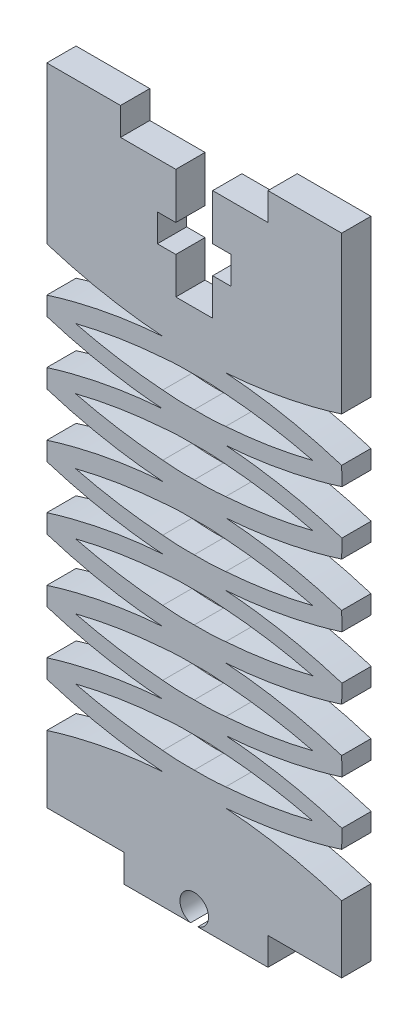
SolidWorks part; units mm, degrees
ref_plane "Front Plane" through (0, 0, 0) normal (0, 0, 1) x (1, 0, 0)
ref_plane "Top Plane" through (0, 0, 0) normal (0, 1, 0) x (1, 0, 0)
ref_plane "Right Plane" through (0, 0, 0) normal (1, 0, 0) x (0, 0, -1)
sketch "Sketch1" plane through (0, 0, 0) normal (0, 0, 1) x (1, 0, 0)
  line L0 (16, 85.8057) -> (16, -11.2855) construction
  line L1 (0, 0) -> (8.3703, 0)
  line L2 (0, 0) -> (0, 7.2655)
  line L3 (0, 70) -> (8, 70)
  line L4 (24, 70) -> (32, 70)
  line L5 (24, 70) -> (24, 67)
  line L6 (24, 67) -> (18, 67)
  line L7 (8, 67) -> (8, 70)
  line L8 (14, 67) -> (14, 62)
  line L9 (14, 55) -> (18, 55)
  line L10 (18, 55) -> (18, 59)
  line L11 (32, 70) -> (32, 53)
  line L12 (12, 62) -> (14, 62)
  line L13 (12, 62) -> (12, 59)
  line L14 (12, 59) -> (14, 59)
  line L15 (20, 62) -> (20, 59)
  line L16 (14, 67) -> (8, 67)
  line L17 (18, 62) -> (20, 62)
  line L18 (14, 59) -> (14, 55)
  line L19 (18, 62) -> (18, 67)
  line L20 (18, 59) -> (20, 59)
  line L21 (40.1078, 53) -> (-4.0863, 53) construction
  line L22 (24, 0) -> (24, -3)
  line L23 (24, -3) -> (16.3905, -3)
  line L24 (8.3703, -3) -> (8.3703, 0)
  line L25 (24, 0) -> (32, 0)
  line L26 (15.6095, -3) -> (8.3703, -3)
  line L27 (26, 0) -> (26, -11.2855) construction
  line L28 (26, 85.8057) -> (26, 8.7935) construction
  line L29 (32, 12.0848) -> (32.0289, 14.0848)
  line L30 (6, 85.8057) -> (6, 8.7935) construction
  line L31 (0, 53) -> (0, 70)
  line L32 (32.0289, 18.904) -> (32, 20.904)
  line L33 (32.0289, 46.1808) -> (32, 48.1808)
  line L34 (32, 5.3702) -> (32, 7.2655)
  line L35 (0, 48.1808) -> (0, 46.1718)
  line L36 (32, 34.5424) -> (32.0289, 32.5424)
  line L37 (32.0289, 27.7232) -> (32, 25.7232)
  line L38 (0, 41.3706) -> (0, 39.3616)
  line L39 (32, 5.3702) -> (32, 0)
  line L40 (0, 34.5424) -> (0, 32.5333)
  line L41 (0, 27.7322) -> (0, 25.7232)
  line L43 (0, 20.904) -> (0, 18.8949)
  line L44 (0, 14.0938) -> (0, 12.0848)
  line L46 (32.0289, 41.3616) -> (32, 39.3616)
  arc A0 (16.3905, -3) -> (15.6095, -3) centre (16, -1.5) ccw
  spline S0 degree 3 poles (32, 53) (27.8985, 51.7075) (23.6915, 50.9043) (19.4175, 50.5904) knots 0 0 0 0 0.790279 0.790279 0.790279 0.790279
  spline S1 degree 3 poles (32, 48.1808) (27.8985, 49.4733) (23.6915, 50.2765) (19.4175, 50.5904) knots 0 0 0 0 0.790279 0.790279 0.790279 0.790279
  spline S2 degree 3 poles (28.8769, 47.068) (26.7129, 47.6104) (23.5714, 48.2011) (20.3909, 48.5189) (19.4167, 48.5904) knots 0.199989 0.199989 0.199989 0.199989 0.610157 0.790279 0.790279 0.790279 0.790279
  spline S3 degree 2 poles (19.4167, 48.5904) (17.7133, 48.7693) (16, 48.7209) knots 0 0 0 1 1 1
  spline S4 degree 2 poles (19.4167, 45.5457) (17.7133, 45.3668) (16, 45.4152) knots 0 0 0 1 1 1
  spline S5 degree 3 poles (28.8769, 47.068) (26.7129, 46.5257) (23.5714, 45.935) (20.3909, 45.6172) (19.4167, 45.5457) knots 0.199989 0.199989 0.199989 0.199989 0.610157 0.790279 0.790279 0.790279 0.790279
  spline S6 degree 3 poles (32.0289, 41.3616) (27.8948, 42.6541) (23.6907, 43.4573) (19.4167, 43.7712) knots 0 0 0 0 0.790279 0.790279 0.790279 0.790279
  spline S7 degree 3 poles (32.0289, 46.1808) (27.8948, 44.8883) (23.6907, 44.0851) (19.4167, 43.7712) knots 0 0 0 0 0.790279 0.790279 0.790279 0.790279
  spline S8 degree 2 poles (19.4167, 41.9967) (17.7133, 42.1756) (16, 42.1272) knots 0 0 0 1 1 1
  spline S9 degree 3 poles (28.8769, 40.4743) (26.7129, 41.0166) (23.5714, 41.6074) (20.3909, 41.9251) (19.4167, 41.9967) knots 0.199989 0.199989 0.199989 0.199989 0.610157 0.790279 0.790279 0.790279 0.790279
  spline S10 degree 2 poles (19.4167, 38.952) (17.7133, 38.7731) (16, 38.8214) knots 0 0 0 1 1 1
  spline S11 degree 3 poles (28.8769, 40.4743) (26.7129, 39.932) (23.5714, 39.3413) (20.3909, 39.0235) (19.4167, 38.952) knots 0.199989 0.199989 0.199989 0.199989 0.610157 0.790279 0.790279 0.790279 0.790279
  spline S12 degree 3 poles (32, 39.3616) (27.8985, 38.0691) (23.6915, 37.2659) (19.4175, 36.952) knots 0 0 0 0 0.790279 0.790279 0.790279 0.790279
  spline S13 degree 3 poles (32.0289, 32.5424) (27.8948, 31.2499) (23.6907, 30.4467) (19.4167, 30.1328) knots 0 0 0 0 0.790279 0.790279 0.790279 0.790279
  spline S14 degree 2 poles (19.4167, 31.9073) (17.7133, 31.7284) (16, 31.7767) knots 0 0 0 1 1 1
  spline S15 degree 3 poles (28.8769, 33.4296) (26.7129, 32.8873) (23.5714, 32.2966) (20.3909, 31.9788) (19.4167, 31.9073) knots 0.199989 0.199989 0.199989 0.199989 0.610157 0.790279 0.790279 0.790279 0.790279
  spline S16 degree 2 poles (19.4167, 34.952) (17.7133, 35.1309) (16, 35.0825) knots 0 0 0 1 1 1
  spline S17 degree 3 poles (28.8769, 33.4296) (26.7129, 33.9719) (23.5714, 34.5627) (20.3909, 34.8804) (19.4167, 34.952) knots 0.199989 0.199989 0.199989 0.199989 0.610157 0.790279 0.790279 0.790279 0.790279
  spline S18 degree 3 poles (32, 34.5424) (27.8985, 35.8349) (23.6915, 36.6381) (19.4175, 36.952) knots 0 0 0 0 0.790279 0.790279 0.790279 0.790279
  spline S19 degree 3 poles (32.0289, 18.904) (27.8948, 17.6114) (23.6907, 16.8082) (19.4167, 16.4944) knots 0 0 0 0 0.790279 0.790279 0.790279 0.790279
  spline S20 degree 2 poles (19.4167, 28.3583) (17.7133, 28.5371) (16, 28.4888) knots 0 0 0 1 1 1
  spline S21 degree 2 poles (19.4167, 25.3136) (17.7133, 25.1347) (16, 25.183) knots 0 0 0 1 1 1
  spline S22 degree 2 poles (19.4167, 21.3136) (17.7133, 21.4924) (16, 21.4441) knots 0 0 0 1 1 1
  spline S23 degree 2 poles (19.4167, 18.2689) (17.7133, 18.09) (16, 18.1383) knots 0 0 0 1 1 1
  spline S24 degree 3 poles (28.8769, 19.7912) (26.7129, 19.2489) (23.5714, 18.6582) (20.3909, 18.3404) (19.4167, 18.2689) knots 0.199989 0.199989 0.199989 0.199989 0.610157 0.790279 0.790279 0.790279 0.790279
  spline S25 degree 3 poles (28.8769, 19.7912) (26.7129, 20.3335) (23.5714, 20.9243) (20.3909, 21.242) (19.4167, 21.3136) knots 0.199989 0.199989 0.199989 0.199989 0.610157 0.790279 0.790279 0.790279 0.790279
  spline S26 degree 3 poles (32, 20.904) (27.8985, 22.1965) (23.6915, 22.9997) (19.4175, 23.3136) knots 0 0 0 0 0.790279 0.790279 0.790279 0.790279
  spline S27 degree 3 poles (32.0289, 27.7232) (27.8948, 29.0157) (23.6907, 29.8189) (19.4167, 30.1328) knots 0 0 0 0 0.790279 0.790279 0.790279 0.790279
  spline S28 degree 3 poles (28.8769, 26.8359) (26.7129, 27.3782) (23.5714, 27.969) (20.3909, 28.2867) (19.4167, 28.3583) knots 0.199989 0.199989 0.199989 0.199989 0.610157 0.790279 0.790279 0.790279 0.790279
  spline S29 degree 3 poles (28.8769, 26.8359) (26.7129, 26.2936) (23.5714, 25.7029) (20.3909, 25.3851) (19.4167, 25.3136) knots 0.199989 0.199989 0.199989 0.199989 0.610157 0.790279 0.790279 0.790279 0.790279
  spline S30 degree 3 poles (32, 25.7232) (27.8985, 24.4306) (23.6915, 23.6274) (19.4175, 23.3136) knots 0 0 0 0 0.790279 0.790279 0.790279 0.790279
  spline S31 degree 3 poles (0, 14.0938) (3.1825, 15.087) (7.361, 15.9984) (11.6091, 16.4228) (12.5833, 16.4944) knots 0.001844 0.001844 0.001844 0.001844 0.610157 0.790279 0.790279 0.790279 0.790279
  spline S32 degree 3 poles (3.1231, 13.1975) (5.2871, 13.7398) (8.4286, 14.3306) (11.6091, 14.6483) (12.5833, 14.7198) knots 0.199989 0.199989 0.199989 0.199989 0.610157 0.790279 0.790279 0.790279 0.790279
  spline S33 degree 2 poles (12.5833, 14.7198) (14.2867, 14.8987) (16, 14.8504) knots 0 0 0 1 1 1
  spline S34 degree 3 poles (3.1231, 13.1975) (5.2871, 12.6552) (8.4286, 12.0644) (11.6091, 11.7467) (12.5833, 11.6752) knots 0.199989 0.199989 0.199989 0.199989 0.610157 0.790279 0.790279 0.790279 0.790279
  spline S35 degree 2 poles (12.5833, 11.6752) (14.2867, 11.4963) (16, 11.5446) knots 0 0 0 1 1 1
  spline S36 degree 3 poles (32, 7.2655) (27.8985, 8.5581) (23.6915, 9.3613) (19.4175, 9.6752) knots 0 0 0 0 0.790279 0.790279 0.790279 0.790279
  spline S37 degree 3 poles (32, 12.0848) (27.8985, 10.7922) (23.6915, 9.989) (19.4175, 9.6752) knots 0 0 0 0 0.790279 0.790279 0.790279 0.790279
  spline S38 degree 2 poles (19.4167, 11.6752) (17.7133, 11.4963) (16, 11.5446) knots 0 0 0 1 1 1
  spline S39 degree 3 poles (28.8769, 13.1975) (26.7129, 12.6552) (23.5714, 12.0644) (20.3909, 11.7467) (19.4167, 11.6752) knots 0.199989 0.199989 0.199989 0.199989 0.610157 0.790279 0.790279 0.790279 0.790279
  spline S40 degree 2 poles (19.4167, 14.7198) (17.7133, 14.8987) (16, 14.8504) knots 0 0 0 1 1 1
  spline S41 degree 3 poles (28.8769, 13.1975) (26.7129, 13.7398) (23.5714, 14.3306) (20.3909, 14.6483) (19.4167, 14.7198) knots 0.199989 0.199989 0.199989 0.199989 0.610157 0.790279 0.790279 0.790279 0.790279
  spline S42 degree 3 poles (32.0289, 14.0848) (27.8948, 15.3773) (23.6907, 16.1805) (19.4167, 16.4944) knots 0 0 0 0 0.790279 0.790279 0.790279 0.790279
  spline S43 degree 3 poles (0, 12.0848) (4.1015, 10.7922) (8.3085, 9.989) (12.5825, 9.6752) knots 0 0 0 0 0.790279 0.790279 0.790279 0.790279
  spline S44 degree 3 poles (0, 7.2655) (4.1015, 8.5581) (8.3085, 9.3613) (12.5825, 9.6752) knots 0 0 0 0 0.790279 0.790279 0.790279 0.790279
  spline S45 degree 3 poles (0, 25.7232) (4.1015, 24.4306) (8.3085, 23.6274) (12.5825, 23.3136) knots 0 0 0 0 0.790279 0.790279 0.790279 0.790279
  spline S46 degree 3 poles (3.1231, 26.8359) (5.2871, 26.2936) (8.4286, 25.7029) (11.6091, 25.3851) (12.5833, 25.3136) knots 0.199989 0.199989 0.199989 0.199989 0.610157 0.790279 0.790279 0.790279 0.790279
  spline S47 degree 3 poles (3.1231, 26.8359) (5.2871, 27.3782) (8.4286, 27.969) (11.6091, 28.2867) (12.5833, 28.3583) knots 0.199989 0.199989 0.199989 0.199989 0.610157 0.790279 0.790279 0.790279 0.790279
  spline S48 degree 3 poles (0, 27.7322) (3.1825, 28.7254) (7.361, 29.6368) (11.6091, 30.0612) (12.5833, 30.1328) knots 0.001844 0.001844 0.001844 0.001844 0.610157 0.790279 0.790279 0.790279 0.790279
  spline S49 degree 3 poles (0, 20.904) (4.1015, 22.1965) (8.3085, 22.9997) (12.5825, 23.3136) knots 0 0 0 0 0.790279 0.790279 0.790279 0.790279
  spline S50 degree 3 poles (3.1231, 19.7912) (5.2871, 20.3335) (8.4286, 20.9243) (11.6091, 21.242) (12.5833, 21.3136) knots 0.199989 0.199989 0.199989 0.199989 0.610157 0.790279 0.790279 0.790279 0.790279
  spline S51 degree 3 poles (3.1231, 19.7912) (5.2871, 19.2489) (8.4286, 18.6582) (11.6091, 18.3404) (12.5833, 18.2689) knots 0.199989 0.199989 0.199989 0.199989 0.610157 0.790279 0.790279 0.790279 0.790279
  spline S52 degree 2 poles (12.5833, 18.2689) (14.2867, 18.09) (16, 18.1383) knots 0 0 0 1 1 1
  spline S53 degree 2 poles (12.5833, 21.3136) (14.2867, 21.4924) (16, 21.4441) knots 0 0 0 1 1 1
  spline S54 degree 2 poles (12.5833, 25.3136) (14.2867, 25.1347) (16, 25.183) knots 0 0 0 1 1 1
  spline S55 degree 2 poles (12.5833, 28.3583) (14.2867, 28.5371) (16, 28.4888) knots 0 0 0 1 1 1
  spline S56 degree 3 poles (0, 18.8949) (3.1825, 17.9018) (7.361, 16.9903) (11.6091, 16.5659) (12.5833, 16.4944) knots 0.001844 0.001844 0.001844 0.001844 0.610157 0.790279 0.790279 0.790279 0.790279
  spline S57 degree 3 poles (0, 34.5424) (4.1015, 35.8349) (8.3085, 36.6381) (12.5825, 36.952) knots 0 0 0 0 0.790279 0.790279 0.790279 0.790279
  spline S58 degree 3 poles (3.1231, 33.4296) (5.2871, 33.9719) (8.4286, 34.5627) (11.6091, 34.8804) (12.5833, 34.952) knots 0.199989 0.199989 0.199989 0.199989 0.610157 0.790279 0.790279 0.790279 0.790279
  spline S59 degree 2 poles (12.5833, 34.952) (14.2867, 35.1309) (16, 35.0825) knots 0 0 0 1 1 1
  spline S60 degree 3 poles (3.1231, 33.4296) (5.2871, 32.8873) (8.4286, 32.2966) (11.6091, 31.9788) (12.5833, 31.9073) knots 0.199989 0.199989 0.199989 0.199989 0.610157 0.790279 0.790279 0.790279 0.790279
  spline S61 degree 2 poles (12.5833, 31.9073) (14.2867, 31.7284) (16, 31.7767) knots 0 0 0 1 1 1
  spline S62 degree 3 poles (0, 32.5333) (3.1825, 31.5402) (7.361, 30.6287) (11.6091, 30.2043) (12.5833, 30.1328) knots 0.001844 0.001844 0.001844 0.001844 0.610157 0.790279 0.790279 0.790279 0.790279
  spline S63 degree 3 poles (0, 39.3616) (4.1015, 38.0691) (8.3085, 37.2659) (12.5825, 36.952) knots 0 0 0 0 0.790279 0.790279 0.790279 0.790279
  spline S64 degree 3 poles (3.1231, 40.4743) (5.2871, 39.932) (8.4286, 39.3413) (11.6091, 39.0235) (12.5833, 38.952) knots 0.199989 0.199989 0.199989 0.199989 0.610157 0.790279 0.790279 0.790279 0.790279
  spline S65 degree 2 poles (12.5833, 38.952) (14.2867, 38.7731) (16, 38.8214) knots 0 0 0 1 1 1
  spline S66 degree 3 poles (3.1231, 40.4743) (5.2871, 41.0166) (8.4286, 41.6074) (11.6091, 41.9251) (12.5833, 41.9967) knots 0.199989 0.199989 0.199989 0.199989 0.610157 0.790279 0.790279 0.790279 0.790279
  spline S67 degree 2 poles (12.5833, 41.9967) (14.2867, 42.1756) (16, 42.1272) knots 0 0 0 1 1 1
  spline S68 degree 3 poles (0, 46.1718) (3.1825, 45.1786) (7.361, 44.2671) (11.6091, 43.8427) (12.5833, 43.7712) knots 0.001844 0.001844 0.001844 0.001844 0.610157 0.790279 0.790279 0.790279 0.790279
  spline S69 degree 3 poles (0, 41.3706) (3.1825, 42.3638) (7.361, 43.2752) (11.6091, 43.6996) (12.5833, 43.7712) knots 0.001844 0.001844 0.001844 0.001844 0.610157 0.790279 0.790279 0.790279 0.790279
  spline S70 degree 3 poles (3.1231, 47.068) (5.2871, 46.5257) (8.4286, 45.935) (11.6091, 45.6172) (12.5833, 45.5457) knots 0.199989 0.199989 0.199989 0.199989 0.610157 0.790279 0.790279 0.790279 0.790279
  spline S71 degree 2 poles (12.5833, 45.5457) (14.2867, 45.3668) (16, 45.4152) knots 0 0 0 1 1 1
  spline S72 degree 2 poles (12.5833, 48.5904) (14.2867, 48.7693) (16, 48.7209) knots 0 0 0 1 1 1
  spline S73 degree 3 poles (3.1231, 47.068) (5.2871, 47.6104) (8.4286, 48.2011) (11.6091, 48.5189) (12.5833, 48.5904) knots 0.199989 0.199989 0.199989 0.199989 0.610157 0.790279 0.790279 0.790279 0.790279
  spline S74 degree 3 poles (0, 48.1808) (4.1015, 49.4733) (8.3085, 50.2765) (12.5825, 50.5904) knots 0 0 0 0 0.790279 0.790279 0.790279 0.790279
  spline S75 degree 3 poles (0, 53) (4.1015, 51.7075) (8.3085, 50.9043) (12.5825, 50.5904) knots 0 0 0 0 0.790279 0.790279 0.790279 0.790279
  point P19 (8, 68.5)
  dimension "D17" = 3.1
  dimension "D1" = 8
  dimension "D2" = 8
  dimension "D3" = 3
  dimension "D4" = 2
  dimension "D5" = 2
  dimension "D6" = 5
  dimension "D7" = 3
  dimension "D8" = 2
  dimension "D9" = 2
  dimension "D10" = 12
  dimension "D11" = 2
  dimension "D12" = 8
  dimension "D13" = 3
  dimension "D14" = 16
  dimension "D15" = 70
  dimension "D16" = 1.5
  dimension "D18" = 2
extrude "Boss-Extrude1" add sketch "Sketch1" along normal blind 3.175
